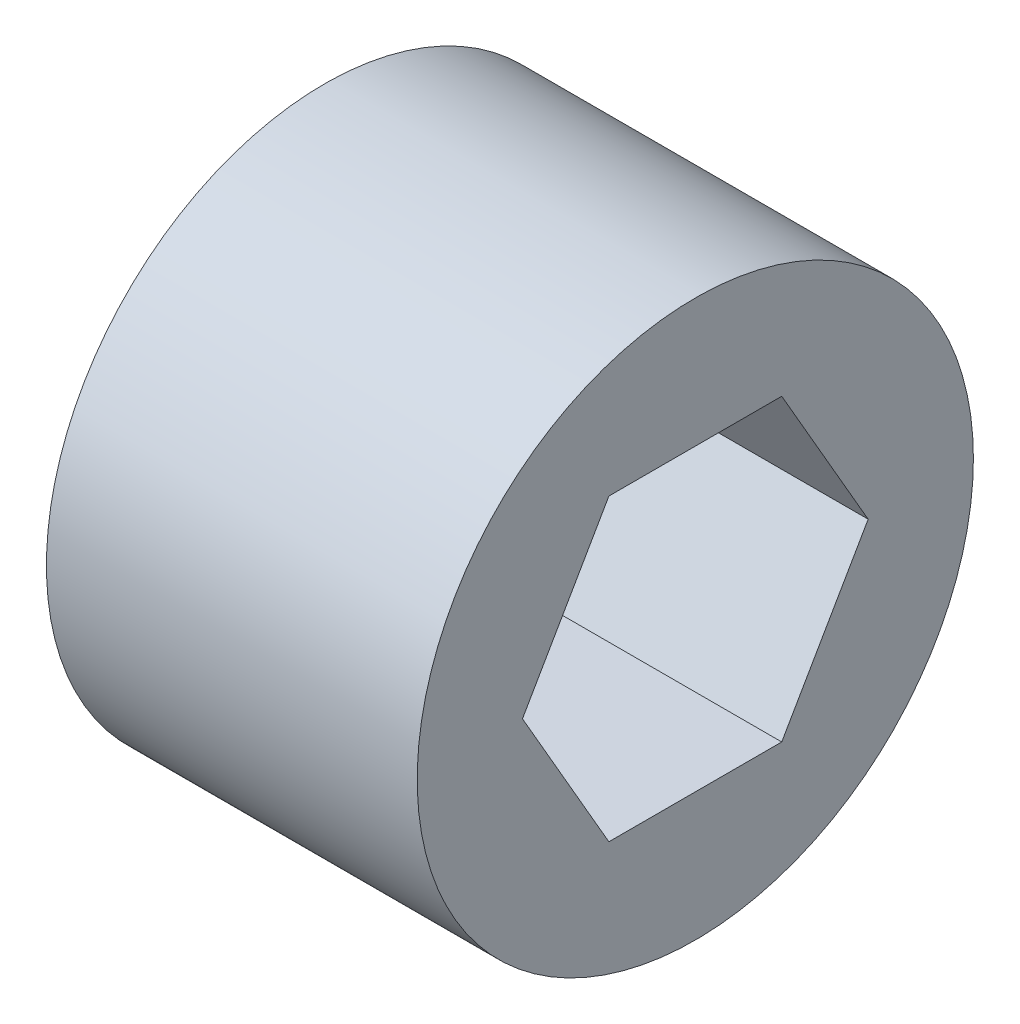
SolidWorks part; units mm, degrees
material "PET"
ref_plane "Front" through (0, 0, 0) normal (0, 0, 1) x (1, 0, 0)
ref_plane "Top" through (0, 0, 0) normal (0, 1, 0) x (1, 0, 0)
ref_plane "Right" through (0, 0, 0) normal (1, 0, 0) x (0, 0, -1)
sketch "Sketch1" plane through (0, 0, 0) normal (1, 0, 0) x (0, 0, -1)
  line L1 (1.48, 2.5635) -> (-1.48, 2.5635)
  line L2 (-1.48, 2.5635) -> (-2.9601, 0)
  line L3 (-2.9601, 0) -> (-1.48, -2.5635)
  line L4 (-1.48, -2.5635) -> (1.48, -2.5635)
  line L5 (1.48, -2.5635) -> (2.9601, 0)
  line L6 (2.9601, 0) -> (1.48, 2.5635)
  circle A0 centre (0, 0) radius 4.7625
  circle A1 centre (0, 0) radius 2.5635 construction
  dimension "D2" = 9.525
  dimension "D1" = 5.127
extrude "Boss-Extrude1" add sketch "Sketch1" along normal blind 6.35
